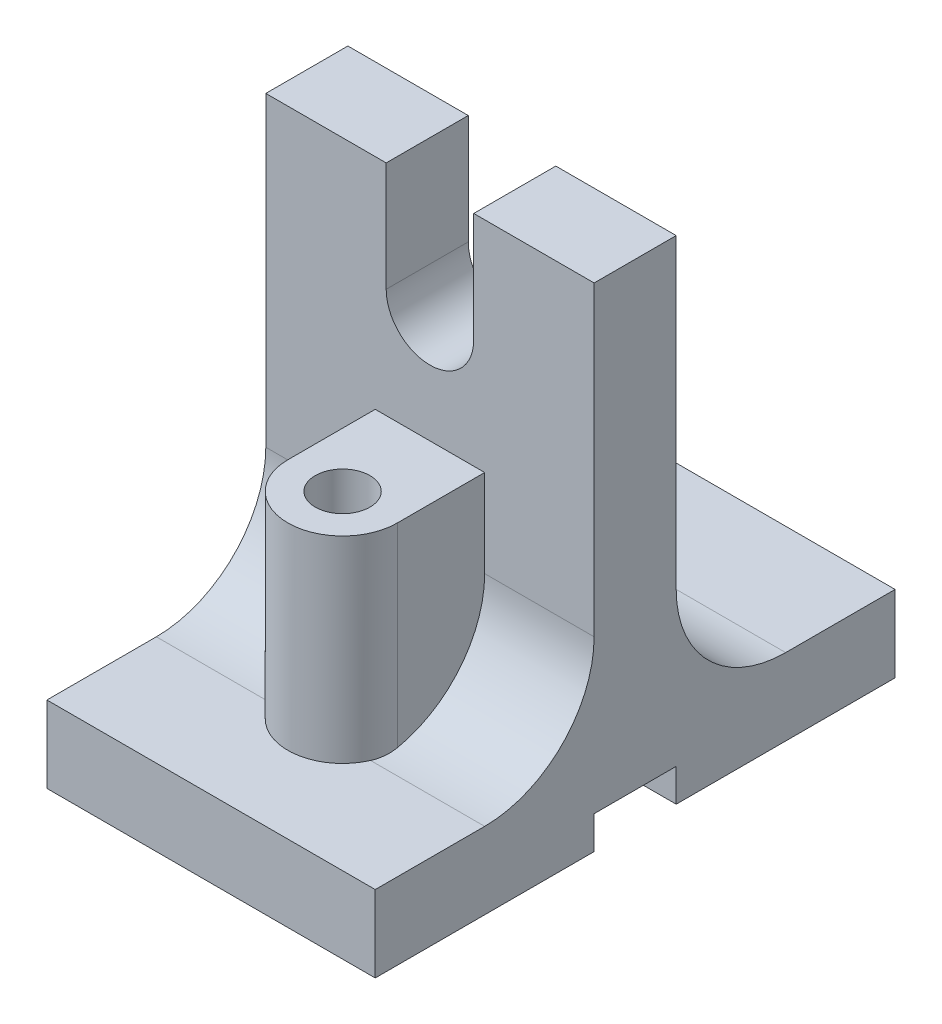
SolidWorks part; units mm, degrees
ref_plane "Front Plane" through (0, 0, 0) normal (0, 0, 1) x (1, 0, 0)
ref_plane "Top Plane" through (0, 0, 0) normal (0, 1, 0) x (1, 0, 0)
ref_plane "Right Plane" through (0, 0, 0) normal (1, 0, 0) x (0, 0, -1)
sketch "Sketch4" plane through (0, 0, 0) normal (1, 0, 0) x (0, 0, -1)
  line L0 (0, 112.9287) -> (0, -59.0625) construction
  line L1 (-98.8636, 0) -> (-7.5, 0) construction
  line L2 (-7.5, 90) -> (7.5, 90)
  line L3 (-47.5, 0) -> (-47.5, 14)
  line L4 (-7.5, 90) -> (-7.5, 34)
  line L5 (7.5, 90) -> (7.5, 34)
  line L6 (-47.5, 0) -> (-7.5, 0)
  line L7 (47.5, 0) -> (47.5, 14)
  line L8 (-47.5, 14) -> (-27.5, 14)
  line L9 (47.5, 14) -> (27.5, 14)
  line L10 (7.5, 0) -> (99.0341, 0) construction
  line L11 (-7.5, 6) -> (7.5, 6)
  line L12 (-7.5, 6) -> (-7.5, 0)
  line L14 (7.5, 6) -> (7.5, 0)
  line L17 (7.5, 0) -> (47.5, 0)
  arc A0 (-7.5, 34) -> (-27.5, 14) centre (-27.5, 34) cw
  arc A1 (7.5, 34) -> (27.5, 14) centre (27.5, 34) ccw
  point P8 (0, 90)
  point P18 (0, 3)
  dimension "D7" = 15
  dimension "D8" = 20
  dimension "D4" = 6
  dimension "D1" = 7.5
  dimension "D2" = 14
  dimension "D3" = 90
  dimension "D5" = 14
  dimension "D6" = 47.5
  dimension "D9" = 7.5
  dimension "D10" = 47.5
  dimension "D11" = 95
extrude "Boss-Extrude1" add sketch "Sketch4" along normal mid plane 60
sketch "Sketch5" plane through (0, 0, 7.5) normal (0, 0, 1) x (1, 0, 0)
  line L0 (30, 90) -> (-30, 90) construction
  line L1 (8, 70) -> (8, 90)
  line L2 (-8, 70) -> (-8, 90)
  line L3 (-8, 90) -> (8, 90)
  arc A0 (-8, 70) -> (8, 70) centre (0, 70) ccw
  dimension "D2" = 16
  dimension "D1" = 20
extrude "Cut-Extrude1" cut sketch "Sketch5" against normal blind 60
ref_plane "Plane3" through (0, 50, 0) normal (0, 1, 0) x (1, 0, 0)
sketch "Sketch6" plane through (0, 50, 0) normal (0, 1, 0) x (1, 0, 0)
  line L0 (-10, -23.4654) -> (-10, -7.5)
  line L1 (30, -7.5) -> (-30, -7.5) construction
  line L2 (10, -23.4654) -> (10, -7.5)
  line L3 (30, -7.5) -> (8, -7.5) construction
  line L4 (-10, -7.5) -> (10, -7.5)
  arc A0 (-10, -23.4654) -> (10, -23.4654) centre (0, -23.4654) ccw
  circle A1 centre (0, -23.4654) radius 5
  dimension "D1" = 20
  dimension "D2" = 10
extrude "Boss-Extrude2" add sketch "Sketch6" against normal up to surface (36 mm away) up to face at (0, 14, 37.5)
